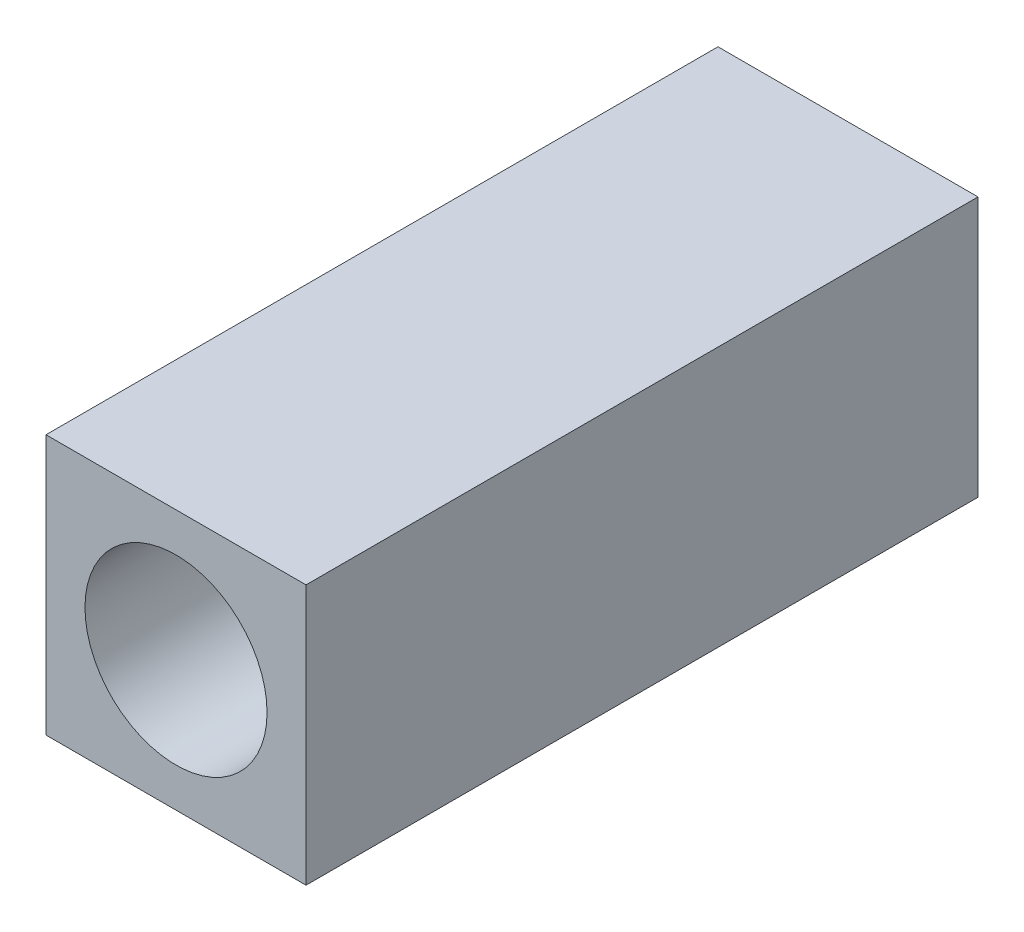
SolidWorks part; units mm, degrees
material "Plain Carbon Steel"
ref_plane "Front Plane" through (0, 0, 0) normal (0, 0, 1) x (1, 0, 0)
ref_plane "Top Plane" through (0, 0, 0) normal (0, 1, 0) x (1, 0, 0)
ref_plane "Right Plane" through (0, 0, 0) normal (1, 0, 0) x (0, 0, -1)
sketch "Sketch1" plane through (0, 0, 0) normal (0, 0, 1) x (1, 0, 0)
  line L1 (-2.999, -3) -> (2.999, -3)
  line L2 (-2.999, -3) -> (-2.999, 3)
  line L3 (-2.999, 3) -> (2.999, 3)
  line L4 (2.999, -3) -> (2.999, 3)
  line L5 (-2.999, -3) -> (2.999, 3) construction
  line L6 (-2.999, 3) -> (2.999, -3) construction
  circle A0 centre (0, 0) radius 3
  dimension "D1" = 6
  dimension "D2" = 3
extrude "Boss-Extrude1" add sketch "Sketch1" along normal blind 16 contours A0 L3 L2 | A0 L4 L3 | L4 A0 L2 | A0 L1 L4 | A0 L2 L1
hole_wizard "M5 Tapped Hole1" positions "Sketch3" profile "Sketch2" tap size "M5" standard "ISO"
sketch "Sketch3" plane through (0, 0, 16) normal (0, 0, 1) x (1, 0, 0)
  point P0 (0, 0)
sketch "Sketch2" plane through (0, 0, 16) normal (1, 0, 0) x (0, -1, 0)
  line L0 (0, 0) -> (0, 15.2618)
  line L1 (0, 15.2618) -> (2.1, 14)
  line L2 (2.1, 14) -> (2.1, 0)
  line L5 (2.1, 0) -> (0, 0)
  line L10 (0, 15.2618) -> (-2.1, 14) construction
  line L11 (0, -6.35) -> (0, 107.95) construction
  dimension "Tap Drill Dia." = 4.2
  dimension "Tap Drill Depth" = 14
  dimension "Drill Angle" = 118
cosmetic thread "Hole Thread1" parameters "D1"=13.2, "D2"=5
chamfer "Chamfer1" distance 0.5 angle 45 4 edges at (-2.999, 0, 0) (0, -3, 0) (2.999, 0, 0) (0, 3, 0)
